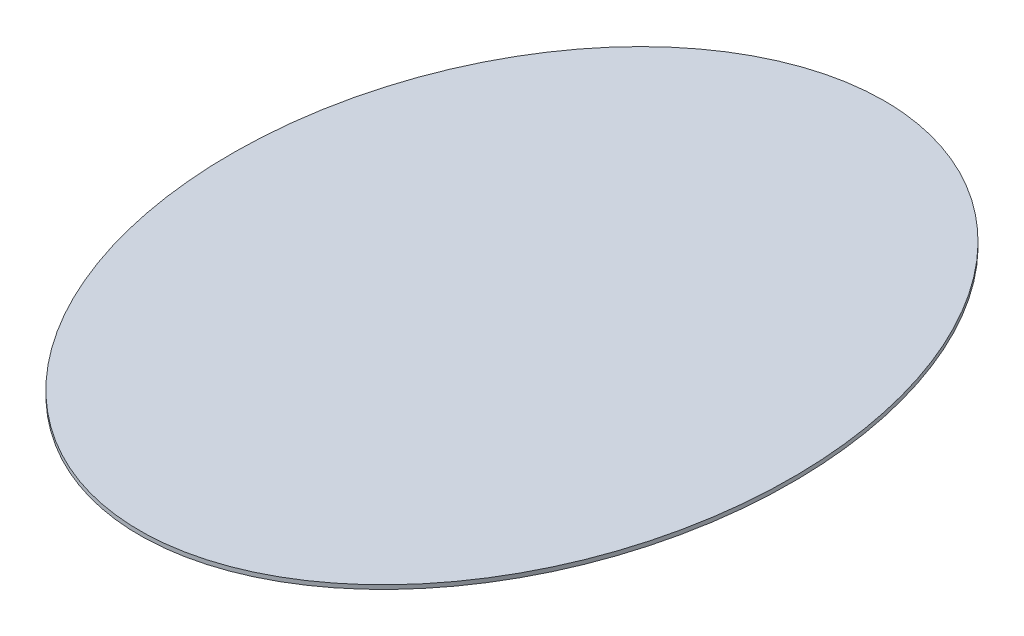
SolidWorks part; units mm, degrees
ref_plane "Front Plane" through (0, 0, 0) normal (0, 0, 1) x (1, 0, 0)
ref_plane "Top Plane" through (0, 0, 0) normal (0, 1, 0) x (1, 0, 0)
ref_plane "Right Plane" through (0, 0, 0) normal (1, 0, 0) x (0, 0, -1)
sketch "Sketch1" plane through (0, 0, 0) normal (0, 1, 0) x (1, 0, 0)
  ellipse E0 centre (0, 0) end of major axis (0, 355) minor radius 265 construction
  ellipse E1 centre (0, 0) end of major axis (0, 365) minor radius 275
  dimension "D1" = 530
  dimension "D2" = 710
  dimension "D3" = 550
  dimension "D4" = 730
extrude "Boss-Extrude1" add sketch "Sketch1" along normal blind 4
